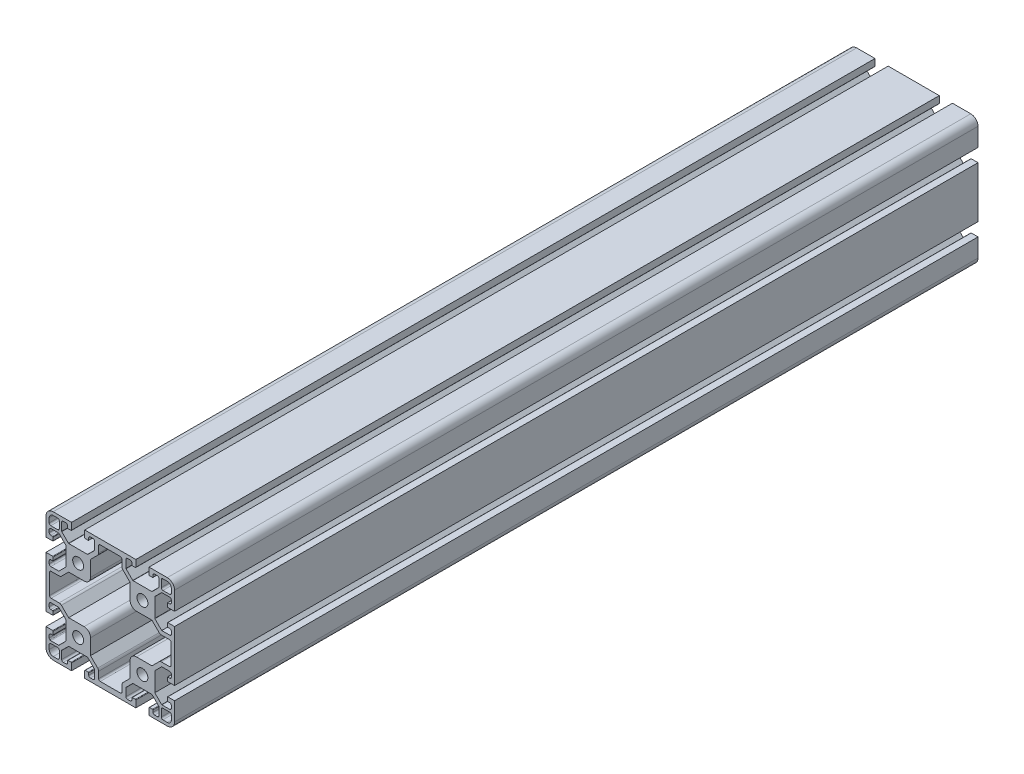
SolidWorks part; units mm, degrees
ref_plane "Front Plane" through (0, 0, 0) normal (0, 0, 1) x (1, 0, 0)
ref_plane "Top Plane" through (0, 0, 0) normal (0, 1, 0) x (1, 0, 0)
ref_plane "Right Plane" through (0, 0, 0) normal (1, 0, 0) x (0, 0, -1)
sketch "Sketch1" plane through (0, 0, 0) normal (0, 0, 1) x (1, 0, 0)
  line L0 (0, 36.8) -> (0, -36.8) construction
  line B0 (-15.9, -35.8) -> (-15.9, -40)
  line B1 (-15.9, -40) -> (15.9, -40)
  line B2 (15.9, -40) -> (15.9, -35.8)
  arc B3 (15.9, -35.8) -> (15.6, -35.5) centre (15.6, -35.8) ccw
  line B4 (15.6, -35.5) -> (13.7, -35.5)
  arc B5 (13.7, -35.5) -> (13.4, -35.8) centre (13.7, -35.8) ccw
  line B6 (13.4, -35.8) -> (13.4, -37)
  arc B7 (12.4, -38) -> (13.4, -37) centre (12.4, -37) ccw
  line B8 (12.4, -38) -> (10.75, -38)
  arc B9 (9.75, -37) -> (10.75, -38) centre (10.75, -37) ccw
  line B10 (9.75, -37) -> (9.75, -32.142)
  arc B11 (9.8379, -31.9299) -> (9.75, -32.142) centre (10.05, -32.142) ccw
  line B12 (9.8379, -31.9299) -> (13.9799, -27.7879)
  arc B13 (14.192, -27.7) -> (13.9799, -27.7879) centre (14.192, -28) ccw
  line B14 (14.192, -27.7) -> (25.808, -27.7)
  arc B15 (26.0201, -27.7879) -> (25.808, -27.7) centre (25.808, -28) ccw
  line B16 (26.0201, -27.7879) -> (30.1621, -31.9299)
  arc B17 (30.25, -32.142) -> (30.1621, -31.9299) centre (29.95, -32.142) ccw
  line B18 (30.25, -32.142) -> (30.25, -37)
  arc B19 (29.25, -38) -> (30.25, -37) centre (29.25, -37) ccw
  line B20 (29.25, -38) -> (27.6, -38)
  arc B21 (26.6, -37) -> (27.6, -38) centre (27.6, -37) ccw
  line B22 (26.6, -37) -> (26.6, -35.8)
  arc B23 (26.6, -35.8) -> (26.3, -35.5) centre (26.3, -35.8) ccw
  line B24 (26.3, -35.5) -> (24.4, -35.5)
  arc B25 (24.4, -35.5) -> (24.1, -35.8) centre (24.4, -35.8) ccw
  line B26 (24.1, -35.8) -> (24.1, -40)
  line B27 (24.1, -40) -> (35.5, -40)
  arc B28 (35.5, -40) -> (40, -35.5) centre (35.5, -35.5) ccw
  line B29 (40, -35.5) -> (40, -24.1)
  line B30 (40, -24.1) -> (35.8, -24.1)
  arc B31 (35.8, -24.1) -> (35.5, -24.4) centre (35.8, -24.4) ccw
  line B32 (35.5, -24.4) -> (35.5, -26.3)
  arc B33 (35.5, -26.3) -> (35.8, -26.6) centre (35.8, -26.3) ccw
  line B34 (35.8, -26.6) -> (37, -26.6)
  arc B35 (38, -27.6) -> (37, -26.6) centre (37, -27.6) ccw
  line B36 (38, -27.6) -> (38, -29.25)
  arc B37 (37, -30.25) -> (38, -29.25) centre (37, -29.25) ccw
  line B38 (37, -30.25) -> (32.142, -30.25)
  arc B39 (31.9299, -30.1621) -> (32.142, -30.25) centre (32.142, -29.95) ccw
  line B40 (31.9299, -30.1621) -> (27.7, -25.9322)
  line B41 (27.7, -25.9322) -> (27.7, -14.0678)
  line B42 (27.7, -14.0678) -> (32.0178, -9.75)
  line B43 (32.0178, -9.75) -> (37, -9.75)
  arc B44 (38, -10.75) -> (37, -9.75) centre (37, -10.75) ccw
  line B45 (38, -10.75) -> (38, -12.4)
  arc B46 (37, -13.4) -> (38, -12.4) centre (37, -12.4) ccw
  line B47 (37, -13.4) -> (35.8, -13.4)
  arc B48 (35.8, -13.4) -> (35.5, -13.7) centre (35.8, -13.7) ccw
  line B49 (35.5, -13.7) -> (35.5, -15.6)
  arc B50 (35.5, -15.6) -> (35.8, -15.9) centre (35.8, -15.6) ccw
  line B51 (35.8, -15.9) -> (40, -15.9)
  line B52 (40, -15.9) -> (40, 15.9)
  line B53 (40, 15.9) -> (35.8, 15.9)
  arc B54 (35.8, 15.9) -> (35.5, 15.6) centre (35.8, 15.6) ccw
  line B55 (35.5, 15.6) -> (35.5, 13.7)
  arc B56 (35.5, 13.7) -> (35.8, 13.4) centre (35.8, 13.7) ccw
  line B57 (35.8, 13.4) -> (37, 13.4)
  arc B58 (38, 12.4) -> (37, 13.4) centre (37, 12.4) ccw
  line B59 (38, 12.4) -> (38, 10.75)
  arc B60 (37, 9.75) -> (38, 10.75) centre (37, 10.75) ccw
  line B61 (37, 9.75) -> (32.0178, 9.75)
  line B62 (32.0178, 9.75) -> (27.7879, 13.9799)
  arc B63 (27.7, 14.192) -> (27.7879, 13.9799) centre (28, 14.192) ccw
  line B64 (27.7, 14.192) -> (27.7, 25.808)
  arc B65 (27.7879, 26.0201) -> (27.7, 25.808) centre (28, 25.808) ccw
  line B66 (27.7879, 26.0201) -> (31.9299, 30.1621)
  arc B67 (32.142, 30.25) -> (31.9299, 30.1621) centre (32.142, 29.95) ccw
  line B68 (32.142, 30.25) -> (37, 30.25)
  arc B69 (38, 29.25) -> (37, 30.25) centre (37, 29.25) ccw
  line B70 (38, 29.25) -> (38, 27.6)
  arc B71 (37, 26.6) -> (38, 27.6) centre (37, 27.6) ccw
  line B72 (37, 26.6) -> (35.8, 26.6)
  arc B73 (35.8, 26.6) -> (35.5, 26.3) centre (35.8, 26.3) ccw
  line B74 (35.5, 26.3) -> (35.5, 24.4)
  arc B75 (35.5, 24.4) -> (35.8, 24.1) centre (35.8, 24.4) ccw
  line B76 (35.8, 24.1) -> (40, 24.1)
  line B77 (40, 24.1) -> (40, 35.5)
  arc B78 (40, 35.5) -> (35.5, 40) centre (35.5, 35.5) ccw
  line B79 (35.5, 40) -> (24.1, 40)
  line B80 (24.1, 40) -> (24.1, 35.8)
  arc B81 (24.1, 35.8) -> (24.4, 35.5) centre (24.4, 35.8) ccw
  line B82 (24.4, 35.5) -> (26.3, 35.5)
  arc B83 (26.3, 35.5) -> (26.6, 35.8) centre (26.3, 35.8) ccw
  line B84 (26.6, 35.8) -> (26.6, 37)
  arc B85 (27.6, 38) -> (26.6, 37) centre (27.6, 37) ccw
  line B86 (27.6, 38) -> (29.25, 38)
  arc B87 (30.25, 37) -> (29.25, 38) centre (29.25, 37) ccw
  line B88 (30.25, 37) -> (30.25, 32.142)
  arc B89 (30.1621, 31.9299) -> (30.25, 32.142) centre (29.95, 32.142) ccw
  line B90 (30.1621, 31.9299) -> (26.0201, 27.7879)
  arc B91 (25.808, 27.7) -> (26.0201, 27.7879) centre (25.808, 28) ccw
  line B92 (25.808, 27.7) -> (14.192, 27.7)
  arc B93 (13.9799, 27.7879) -> (14.192, 27.7) centre (14.192, 28) ccw
  line B94 (13.9799, 27.7879) -> (9.8379, 31.9299)
  arc B95 (9.75, 32.142) -> (9.8379, 31.9299) centre (10.05, 32.142) ccw
  line B96 (9.75, 32.142) -> (9.75, 37)
  arc B97 (10.75, 38) -> (9.75, 37) centre (10.75, 37) ccw
  line B98 (10.75, 38) -> (12.4, 38)
  arc B99 (13.4, 37) -> (12.4, 38) centre (12.4, 37) ccw
  line B100 (13.4, 37) -> (13.4, 35.8)
  arc B101 (13.4, 35.8) -> (13.7, 35.5) centre (13.7, 35.8) ccw
  line B102 (13.7, 35.5) -> (15.6, 35.5)
  arc B103 (15.6, 35.5) -> (15.9, 35.8) centre (15.6, 35.8) ccw
  line B104 (15.9, 35.8) -> (15.9, 40)
  line B105 (15.9, 40) -> (-15.9, 40)
  line B106 (-15.9, 40) -> (-15.9, 35.8)
  arc B107 (-15.9, 35.8) -> (-15.6, 35.5) centre (-15.6, 35.8) ccw
  line B108 (-15.6, 35.5) -> (-13.7, 35.5)
  arc B109 (-13.7, 35.5) -> (-13.4, 35.8) centre (-13.7, 35.8) ccw
  line B110 (-13.4, 35.8) -> (-13.4, 37)
  arc B111 (-12.4, 38) -> (-13.4, 37) centre (-12.4, 37) ccw
  line B112 (-12.4, 38) -> (-10.75, 38)
  arc B113 (-9.75, 37) -> (-10.75, 38) centre (-10.75, 37) ccw
  line B114 (-9.75, 37) -> (-9.75, 32.142)
  arc B115 (-9.8379, 31.9299) -> (-9.75, 32.142) centre (-10.05, 32.142) ccw
  line B116 (-9.8379, 31.9299) -> (-13.9799, 27.7879)
  arc B117 (-14.192, 27.7) -> (-13.9799, 27.7879) centre (-14.192, 28) ccw
  line B118 (-14.192, 27.7) -> (-25.808, 27.7)
  arc B119 (-26.0201, 27.7879) -> (-25.808, 27.7) centre (-25.808, 28) ccw
  line B120 (-26.0201, 27.7879) -> (-30.1621, 31.9299)
  arc B121 (-30.25, 32.142) -> (-30.1621, 31.9299) centre (-29.95, 32.142) ccw
  line B122 (-30.25, 32.142) -> (-30.25, 37)
  arc B123 (-29.25, 38) -> (-30.25, 37) centre (-29.25, 37) ccw
  line B124 (-29.25, 38) -> (-27.6, 38)
  arc B125 (-26.6, 37) -> (-27.6, 38) centre (-27.6, 37) ccw
  line B126 (-26.6, 37) -> (-26.6, 35.8)
  arc B127 (-26.6, 35.8) -> (-26.3, 35.5) centre (-26.3, 35.8) ccw
  line B128 (-26.3, 35.5) -> (-24.4, 35.5)
  arc B129 (-24.4, 35.5) -> (-24.1, 35.8) centre (-24.4, 35.8) ccw
  line B130 (-24.1, 35.8) -> (-24.1, 40)
  line B131 (-24.1, 40) -> (-35.5, 40)
  arc B132 (-35.5, 40) -> (-40, 35.5) centre (-35.5, 35.5) ccw
  line B133 (-40, 35.5) -> (-40, 24.1)
  line B134 (-40, 24.1) -> (-35.8, 24.1)
  arc B135 (-35.8, 24.1) -> (-35.5, 24.4) centre (-35.8, 24.4) ccw
  line B136 (-35.5, 24.4) -> (-35.5, 26.3)
  arc B137 (-35.5, 26.3) -> (-35.8, 26.6) centre (-35.8, 26.3) ccw
  line B138 (-35.8, 26.6) -> (-37, 26.6)
  arc B139 (-38, 27.6) -> (-37, 26.6) centre (-37, 27.6) ccw
  line B140 (-38, 27.6) -> (-38, 29.25)
  arc B141 (-37, 30.25) -> (-38, 29.25) centre (-37, 29.25) ccw
  line B142 (-37, 30.25) -> (-32.142, 30.25)
  arc B143 (-31.9299, 30.1621) -> (-32.142, 30.25) centre (-32.142, 29.95) ccw
  line B144 (-31.9299, 30.1621) -> (-27.7879, 26.0201)
  arc B145 (-27.7, 25.808) -> (-27.7879, 26.0201) centre (-28, 25.808) ccw
  line B146 (-27.7, 25.808) -> (-27.7, 14.192)
  arc B147 (-27.7879, 13.9799) -> (-27.7, 14.192) centre (-28, 14.192) ccw
  line B148 (-27.7879, 13.9799) -> (-32.0178, 9.75)
  line B149 (-32.0178, 9.75) -> (-37, 9.75)
  arc B150 (-38, 10.75) -> (-37, 9.75) centre (-37, 10.75) ccw
  line B151 (-38, 10.75) -> (-38, 12.4)
  arc B152 (-37, 13.4) -> (-38, 12.4) centre (-37, 12.4) ccw
  line B153 (-37, 13.4) -> (-35.8, 13.4)
  arc B154 (-35.8, 13.4) -> (-35.5, 13.7) centre (-35.8, 13.7) ccw
  line B155 (-35.5, 13.7) -> (-35.5, 15.6)
  arc B156 (-35.5, 15.6) -> (-35.8, 15.9) centre (-35.8, 15.6) ccw
  line B157 (-35.8, 15.9) -> (-40, 15.9)
  line B158 (-40, 15.9) -> (-40, -15.9)
  line B159 (-40, -15.9) -> (-35.8, -15.9)
  arc B160 (-35.8, -15.9) -> (-35.5, -15.6) centre (-35.8, -15.6) ccw
  line B161 (-35.5, -15.6) -> (-35.5, -13.7)
  arc B162 (-35.5, -13.7) -> (-35.8, -13.4) centre (-35.8, -13.7) ccw
  line B163 (-35.8, -13.4) -> (-37, -13.4)
  arc B164 (-38, -12.4) -> (-37, -13.4) centre (-37, -12.4) ccw
  line B165 (-38, -12.4) -> (-38, -10.75)
  arc B166 (-37, -9.75) -> (-38, -10.75) centre (-37, -10.75) ccw
  line B167 (-37, -9.75) -> (-32.0178, -9.75)
  line B168 (-32.0178, -9.75) -> (-27.7879, -13.9799)
  arc B169 (-27.7, -14.192) -> (-27.7879, -13.9799) centre (-28, -14.192) ccw
  line B170 (-27.7, -14.192) -> (-27.7, -25.808)
  arc B171 (-27.7879, -26.0201) -> (-27.7, -25.808) centre (-28, -25.808) ccw
  line B172 (-27.7879, -26.0201) -> (-31.9299, -30.1621)
  arc B173 (-32.142, -30.25) -> (-31.9299, -30.1621) centre (-32.142, -29.95) ccw
  line B174 (-32.142, -30.25) -> (-37, -30.25)
  arc B175 (-37.582, -30.0632) -> (-37, -30.25) centre (-37, -29.25) ccw
  spline B176 degree 3 poles (-37.582, -30.0632) (-37.5892, -30.058) (-37.5963, -30.0528) (-37.6034, -30.0475) knots 0 0 0 0 1 1 1 1
  arc B177 (-38, -29.25) -> (-37.6034, -30.0475) centre (-37, -29.25) ccw
  line B178 (-38, -29.25) -> (-38, -27.6)
  arc B179 (-37, -26.6) -> (-38, -27.6) centre (-37, -27.6) ccw
  line B180 (-37, -26.6) -> (-35.8, -26.6)
  arc B181 (-35.8, -26.6) -> (-35.5, -26.3) centre (-35.8, -26.3) ccw
  line B182 (-35.5, -26.3) -> (-35.5, -24.4)
  arc B183 (-35.5, -24.4) -> (-35.8, -24.1) centre (-35.8, -24.4) ccw
  line B184 (-35.8, -24.1) -> (-40, -24.1)
  line B185 (-40, -24.1) -> (-40, -35.5)
  arc B186 (-40, -35.5) -> (-35.5, -40) centre (-35.5, -35.5) ccw
  line B187 (-35.5, -40) -> (-24.1, -40)
  line B188 (-24.1, -40) -> (-24.1, -35.8)
  arc B189 (-24.1, -35.8) -> (-24.4, -35.5) centre (-24.4, -35.8) ccw
  line B190 (-24.4, -35.5) -> (-26.3, -35.5)
  arc B191 (-26.3, -35.5) -> (-26.6, -35.8) centre (-26.3, -35.8) ccw
  line B192 (-26.6, -35.8) -> (-26.6, -37)
  arc B193 (-27.6, -38) -> (-26.6, -37) centre (-27.6, -37) ccw
  line B194 (-27.6, -38) -> (-29.25, -38)
  arc B195 (-30.25, -37) -> (-29.25, -38) centre (-29.25, -37) ccw
  line B196 (-30.25, -37) -> (-30.25, -32.142)
  arc B197 (-30.1621, -31.9299) -> (-30.25, -32.142) centre (-29.95, -32.142) ccw
  line B198 (-30.1621, -31.9299) -> (-26.0201, -27.7879)
  arc B199 (-25.808, -27.7) -> (-26.0201, -27.7879) centre (-25.808, -28) ccw
  line B200 (-25.808, -27.7) -> (-14.192, -27.7)
  arc B201 (-13.9799, -27.7879) -> (-14.192, -27.7) centre (-14.192, -28) ccw
  line B202 (-13.9799, -27.7879) -> (-9.8379, -31.9299)
  arc B203 (-9.75, -32.142) -> (-9.8379, -31.9299) centre (-10.05, -32.142) ccw
  line B204 (-9.75, -32.142) -> (-9.75, -37)
  arc B205 (-10.75, -38) -> (-9.75, -37) centre (-10.75, -37) ccw
  line B206 (-10.75, -38) -> (-12.4, -38)
  arc B207 (-13.4, -37) -> (-12.4, -38) centre (-12.4, -37) ccw
  line B208 (-13.4, -37) -> (-13.4, -35.8)
  arc B209 (-13.4, -35.8) -> (-13.7, -35.5) centre (-13.7, -35.8) ccw
  line B210 (-13.7, -35.5) -> (-15.6, -35.5)
  arc B211 (-15.6, -35.5) -> (-15.9, -35.8) centre (-15.6, -35.8) ccw
  circle B212 centre (-20, -20) radius 3.4
  line B213 (-7.8358, 30.3964) -> (-12.3, 25.9322)
  line B214 (-12.3, 25.9322) -> (-12.3, 16.3)
  arc B215 (-16.3, 12.3) -> (-12.3, 16.3) centre (-16.3, 16.3) ccw
  line B216 (-16.3, 12.3) -> (-25.9322, 12.3)
  line B217 (-25.9322, 12.3) -> (-30.3964, 7.8358)
  arc B218 (-31.8107, 7.25) -> (-30.3964, 7.8358) centre (-31.8107, 9.25) ccw
  line B219 (-31.8107, 7.25) -> (-36.8, 7.25)
  arc B220 (-36.8, 7.25) -> (-37.8, 6.25) centre (-36.8, 6.25) ccw
  line B221 (-37.8, 6.25) -> (-37.8, -6.25)
  arc B222 (-37.8, -6.25) -> (-36.8, -7.25) centre (-36.8, -6.25) ccw
  line B223 (-36.8, -7.25) -> (-31.8107, -7.25)
  arc B224 (-30.3964, -7.8358) -> (-31.8107, -7.25) centre (-31.8107, -9.25) ccw
  line B225 (-30.3964, -7.8358) -> (-25.9322, -12.3)
  line B226 (-25.9322, -12.3) -> (-16.3, -12.3)
  arc B227 (-12.3, -16.3) -> (-16.3, -12.3) centre (-16.3, -16.3) ccw
  line B228 (-12.3, -16.3) -> (-12.3, -25.9322)
  line B229 (-12.3, -25.9322) -> (-7.8358, -30.3964)
  arc B230 (-7.25, -31.8107) -> (-7.8358, -30.3964) centre (-9.25, -31.8107) ccw
  line B231 (-7.25, -31.8107) -> (-7.25, -35.8)
  arc B232 (-7.25, -35.8) -> (-6.25, -36.8) centre (-6.25, -35.8) ccw
  line B233 (-6.25, -36.8) -> (6.25, -36.8)
  arc B234 (6.25, -36.8) -> (7.25, -35.8) centre (6.25, -35.8) ccw
  line B235 (7.25, -35.8) -> (7.25, -31.8107)
  arc B236 (7.8358, -30.3964) -> (7.25, -31.8107) centre (9.25, -31.8107) ccw
  line B237 (7.8358, -30.3964) -> (12.3, -25.9322)
  line B238 (12.3, -25.9322) -> (12.3, -16.3)
  arc B239 (16.3, -12.3) -> (12.3, -16.3) centre (16.3, -16.3) ccw
  line B240 (16.3, -12.3) -> (25.9322, -12.3)
  line B241 (25.9322, -12.3) -> (30.3964, -7.8358)
  arc B242 (31.8107, -7.25) -> (30.3964, -7.8358) centre (31.8107, -9.25) ccw
  line B243 (31.8107, -7.25) -> (36.8, -7.25)
  arc B244 (36.8, -7.25) -> (37.8, -6.25) centre (36.8, -6.25) ccw
  line B245 (37.8, -6.25) -> (37.8, 6.25)
  arc B246 (37.8, 6.25) -> (36.8, 7.25) centre (36.8, 6.25) ccw
  line B247 (36.8, 7.25) -> (31.8107, 7.25)
  arc B248 (30.3964, 7.8358) -> (31.8107, 7.25) centre (31.8107, 9.25) ccw
  line B249 (30.3964, 7.8358) -> (25.9322, 12.3)
  line B250 (25.9322, 12.3) -> (16.3, 12.3)
  arc B251 (12.3, 16.3) -> (16.3, 12.3) centre (16.3, 16.3) ccw
  line B252 (12.3, 16.3) -> (12.3, 25.9322)
  line B253 (12.3, 25.9322) -> (7.8358, 30.3964)
  arc B254 (7.25, 31.8107) -> (7.8358, 30.3964) centre (9.25, 31.8107) ccw
  line B255 (7.25, 31.8107) -> (7.25, 35.8)
  arc B256 (7.25, 35.8) -> (6.25, 36.8) centre (6.25, 35.8) ccw
  line B257 (6.25, 36.8) -> (-6.25, 36.8)
  arc B258 (-6.25, 36.8) -> (-7.25, 35.8) centre (-6.25, 35.8) ccw
  line B259 (-7.25, 35.8) -> (-7.25, 31.8107)
  arc B260 (-7.8358, 30.3964) -> (-7.25, 31.8107) centre (-9.25, 31.8107) ccw
  line B261 (-32.75, -31.75) -> (-37, -31.75)
  arc B262 (-37, -31.75) -> (-38, -32.75) centre (-37, -32.75) ccw
  line B263 (-38, -32.75) -> (-38, -35.5)
  arc B264 (-38, -35.5) -> (-35.5, -38) centre (-35.5, -35.5) ccw
  line B265 (-35.5, -38) -> (-32.75, -38)
  arc B266 (-32.75, -38) -> (-31.75, -37) centre (-32.75, -37) ccw
  line B267 (-31.75, -37) -> (-31.75, -32.75)
  arc B268 (-31.75, -32.75) -> (-32.75, -31.75) centre (-32.75, -32.75) ccw
  line B269 (-31.75, 32.75) -> (-31.75, 37)
  arc B270 (-31.75, 37) -> (-32.75, 38) centre (-32.75, 37) ccw
  line B271 (-32.75, 38) -> (-35.5, 38)
  arc B272 (-35.5, 38) -> (-38, 35.5) centre (-35.5, 35.5) ccw
  line B273 (-38, 35.5) -> (-38, 32.75)
  arc B274 (-38, 32.75) -> (-37, 31.75) centre (-37, 32.75) ccw
  line B275 (-37, 31.75) -> (-32.75, 31.75)
  arc B276 (-32.75, 31.75) -> (-31.75, 32.75) centre (-32.75, 32.75) ccw
  line B277 (31.75, -32.75) -> (31.75, -37)
  arc B278 (31.75, -37) -> (32.75, -38) centre (32.75, -37) ccw
  line B279 (32.75, -38) -> (35.5, -38)
  arc B280 (35.5, -38) -> (38, -35.5) centre (35.5, -35.5) ccw
  line B281 (38, -35.5) -> (38, -32.75)
  arc B282 (38, -32.75) -> (37, -31.75) centre (37, -32.75) ccw
  line B283 (37, -31.75) -> (32.75, -31.75)
  arc B284 (32.75, -31.75) -> (31.75, -32.75) centre (32.75, -32.75) ccw
  circle B285 centre (20, 20) radius 3.4
  circle B286 centre (-20, 20) radius 3.4
  line B287 (32.75, 31.75) -> (37, 31.75)
  arc B288 (37, 31.75) -> (38, 32.75) centre (37, 32.75) ccw
  line B289 (38, 32.75) -> (38, 35.5)
  arc B290 (38, 35.5) -> (35.5, 38) centre (35.5, 35.5) ccw
  line B291 (35.5, 38) -> (32.75, 38)
  arc B292 (32.75, 38) -> (31.75, 37) centre (32.75, 37) ccw
  line B293 (31.75, 37) -> (31.75, 32.75)
  arc B294 (31.75, 32.75) -> (32.75, 31.75) centre (32.75, 32.75) ccw
  circle B295 centre (20, -20) radius 3.4
sketch_block_instance "S8-8080-1"
sketch_block "S8-8080"
extrude "Boss-Extrude1" add sketch "Sketch1" along normal blind 500
